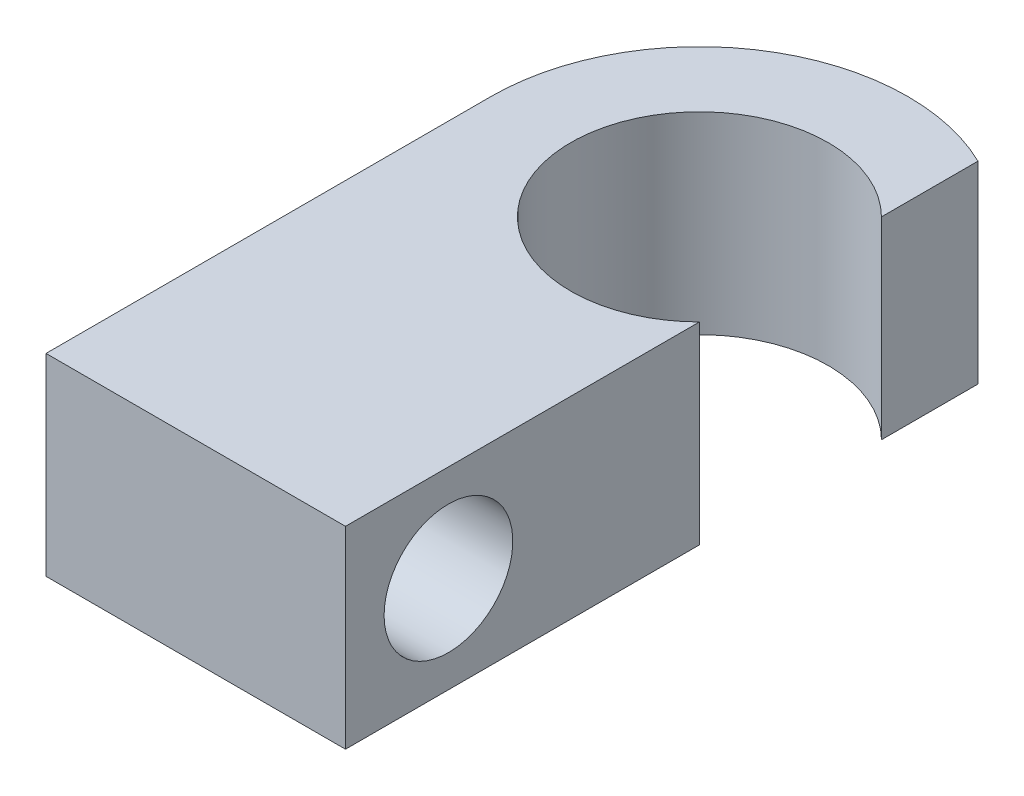
SolidWorks part; units mm, degrees
ref_plane "Front Plane" through (0, 0, 0) normal (0, 0, 1) x (1, 0, 0)
ref_plane "Top Plane" through (0, 0, 0) normal (0, 1, 0) x (1, 0, 0)
ref_plane "Right Plane" through (0, 0, 0) normal (1, 0, 0) x (0, 0, -1)
sketch "Sketch1" plane through (0, 0, 0) normal (0, 1, 0) x (1, 0, 0)
  line L0 (0, 0) -> (4.4901, 4.4901) construction
  line L1 (0, 0) -> (4.4901, -4.4901) construction
  line L2 (4.4901, 4.4901) -> (4.4901, 9.2526)
  line L3 (4.4901, -4.4901) -> (4.4901, -9.2526)
  arc A0 (4.4901, 4.4901) -> (4.4901, -4.4901) centre (0, 0) ccw
  arc A1 (4.4901, 9.2526) -> (4.4901, -9.2526) centre (0, 0) ccw
  dimension "D1" = 12.7
  dimension "D2" = 90
  dimension "D3" = 4.7625
extrude "Boss-Extrude1" add sketch "Sketch1" along normal blind 9.525
sketch "Sketch2" plane through (0, 9.525, 0) normal (0, 1, 0) x (1, 0, 0)
  line L0 (-10.2846, 0) -> (-10.2846, -21.9526)
  line L1 (-10.2846, -21.9526) -> (4.4901, -21.9526)
  line L2 (4.4901, -21.9526) -> (4.4901, -9.2526)
  line L3 (4.4901, -9.2526) -> (4.4901, -4.4901) construction
  arc A0 (4.4901, 9.2526) -> (4.4901, -9.2526) centre (0, 0) ccw construction
  arc A1 (-10.2846, 0) -> (4.4901, -9.2526) centre (0, 0) ccw
  dimension "D1" = 12.7
extrude "Boss-Extrude2" add sketch "Sketch2" against normal through all
sketch "Sketch3" plane through (-10.2846, 0, 0) normal (-1, 0, 0) x (0, 0, 1)
  line L0 (21.9526, 0) -> (21.9526, 9.525) construction
  line L1 (0, 0) -> (0, 9.525) construction
  circle A0 centre (16.8726, 4.7625) radius 3.175
  point P4 (21.9526, 4.7625)
  dimension "D1" = 6.35
  dimension "D2" = 5.08
extrude "Cut-Extrude1" cut sketch "Sketch3" against normal through all
